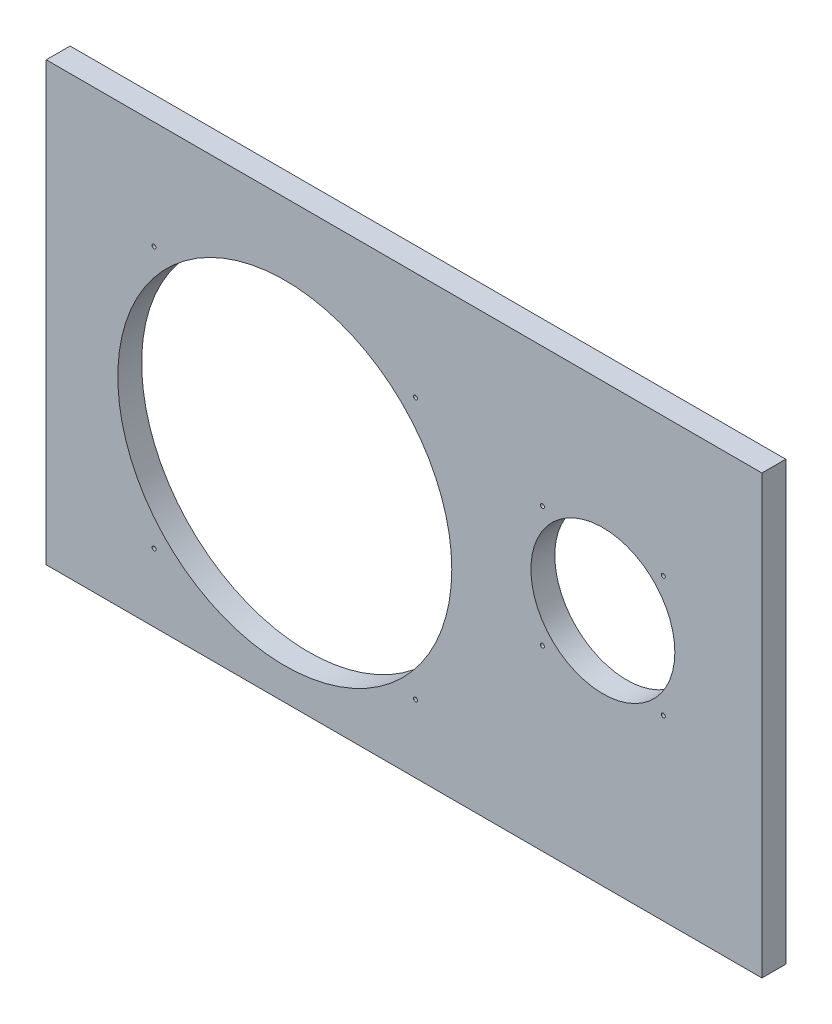
SolidWorks part; units mm, degrees
ref_plane "Front Plane" through (0, 0, 0) normal (0, 0, 1) x (1, 0, 0)
ref_plane "Top Plane" through (0, 0, 0) normal (0, 1, 0) x (1, 0, 0)
ref_plane "Right Plane" through (0, 0, 0) normal (1, 0, 0) x (0, 0, -1)
sketch "Sketch1" plane through (0, 0, 0) normal (0, 0, 1) x (1, 0, 0)
  line L1 (0, 0) -> (180, 0)
  line L2 (0, 0) -> (0, 110)
  line L3 (0, 110) -> (180, 110)
  line L4 (180, 0) -> (180, 110)
  circle A0 centre (60, 50) radius 42
  circle A1 centre (140, 60) radius 18.1
extrude "Boss-Extrude1" add sketch "Sketch1" along normal blind 6
sketch "Sketch2" plane through (0, 0, 0) normal (0, 0, 1) x (1, 0, 0)
  point P0 (60, 50)
sketch "Sketch3" plane through (0, 0, 0) normal (0, 0, 1) x (1, 0, 0)
  line L0 (60, 50) -> (92.8805, 82.8805) construction
  line L1 (60, 50) -> (27.1195, 82.8805) construction
  line L2 (60, 50) -> (27.1195, 17.1195) construction
  line L3 (60, 50) -> (92.8805, 17.1195) construction
  line L4 (140, 60) -> (155.2028, 75.2028) construction
  line L5 (155.2028, 75.2028) -> (140, 60) construction
  line L6 (124.7972, 75.2028) -> (140, 60) construction
  line L7 (140, 60) -> (124.7972, 44.7972) construction
  line L8 (124.7972, 44.7972) -> (140, 60) construction
  line L9 (155.2028, 44.7972) -> (140, 60) construction
  line L10 (140, 60) -> (139.5199, 60.5643)
  circle A0 centre (92.8805, 82.8805) radius 0.5
  circle A1 centre (27.1195, 82.8805) radius 0.5
  circle A2 centre (27.1195, 17.1195) radius 0.5
  circle A3 centre (92.8805, 17.1195) radius 0.5
  circle A4 centre (155.2028, 75.2028) radius 0.5
  circle A5 centre (124.7972, 75.2028) radius 0.5
  circle A6 centre (124.7972, 44.7972) radius 0.5
  circle A7 centre (155.2028, 44.7972) radius 0.5
extrude "Cut-Extrude1" cut sketch "Sketch3" along normal blind 30 contours A1 | A0 | A2 | A3 | A6 | A5 | A4 | A7
